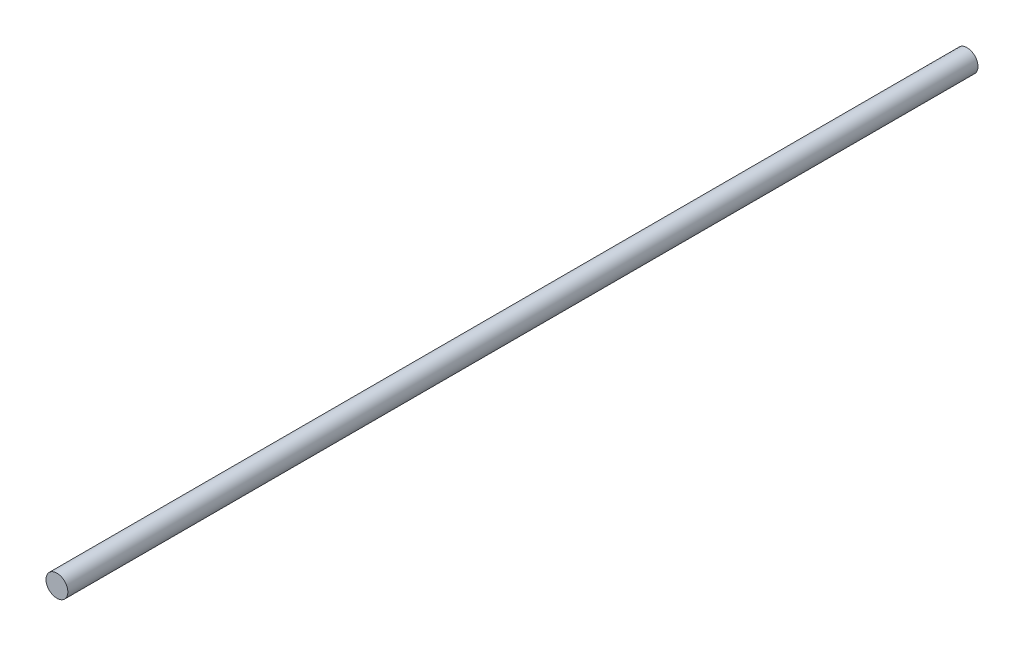
SolidWorks part; units mm, degrees
ref_plane "Front Plane" through (0, 0, 0) normal (0, 0, 1) x (1, 0, 0)
ref_plane "Top Plane" through (0, 0, 0) normal (0, 1, 0) x (1, 0, 0)
ref_plane "Right Plane" through (0, 0, 0) normal (1, 0, 0) x (0, 0, -1)
sketch "Sketch1" plane through (0, 0, 0) normal (0, 0, 1) x (1, 0, 0)
  circle A0 centre (0, 0) radius 6
  dimension "D1" = 12
extrude "Boss-Extrude1" add sketch "Sketch1" along normal blind 500
